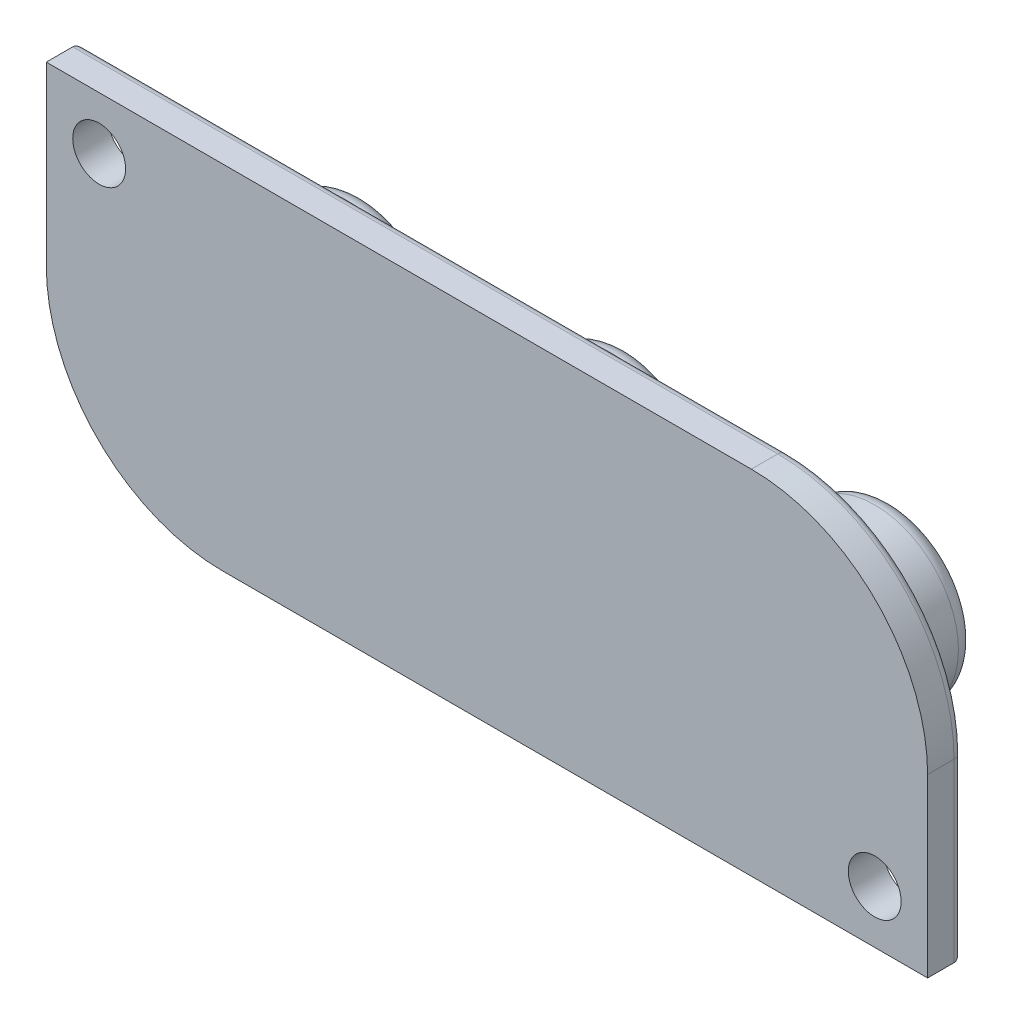
SolidWorks part; units mm, degrees
ref_plane "Alzado" through (0, 0, 0) normal (0, 0, 1) x (1, 0, 0)
ref_plane "Planta" through (0, 0, 0) normal (0, 1, 0) x (1, 0, 0)
ref_plane "Vista lateral" through (0, 0, 0) normal (1, 0, 0) x (0, 0, -1)
sketch "Croquis1" plane through (0, 0, 0) normal (0, 0, 1) x (1, 0, 0)
  line L4 (77.5, 27.5) -> (77.5, 24.2463) construction
  line L5 (52.5, 37.5) -> (102.5, 37.5)
  line L7 (52.5, 17.5) -> (102.5, 17.5)
  line L8 (102.5, 37.5) -> (102.5, 17.5)
  line L10 (52.5, 27.5) -> (102.5, 27.5) construction
  line L11 (52.5, 37.5) -> (52.5, 17.5)
  point P0 (92.5, 27.5)
  dimension "D1" = 20
  dimension "D2" = 50
extrude "Saliente-Extruir1" add sketch "Croquis1" along normal blind 2
sketch "Croquis2" plane through (0, 0, 0) normal (0, 0, -1) x (-1, 0, 0)
  line L0 (-92.5, 27.5) -> (-77.5, 27.5) construction
  circle A4 centre (-92.5, 27.5) radius 4.75
  circle A5 centre (-77.5, 27.5) radius 4.75
  circle A6 centre (-62.5, 27.5) radius 4.75
  dimension "D1" = 9.5
  dimension "D2" = 15
extrude "Saliente-Extruir2" add sketch "Croquis2" along normal blind 6
sketch "Croquis3" plane through (0, 0, 0) normal (0, 0, -1) x (-1, 0, 0)
  line L5 (-86.8264, 25) -> (-68.1736, 30) construction
  line L6 (-86.8264, 30) -> (-68.1736, 25) construction
  line L10 (-85.748, 30) -> (-87.7924, 30.8017) construction
  line L11 (-87.7924, 30.8017) -> (-86.8264, 30) construction
  line L12 (-86.8264, 30) -> (-86.6329, 30.8376) construction
  arc A0 (-87.3586, 30.0746) -> (-86.4645, 30.5224) centre (-86.9115, 30.2985) ccw
  arc A1 (-86.4645, 24.4776) -> (-87.3586, 24.9254) centre (-86.9115, 24.7015) ccw
  arc A2 (-82.6414, 24.9254) -> (-83.5355, 24.4776) centre (-83.0885, 24.7015) ccw
  arc A3 (-83.5355, 30.5224) -> (-82.6414, 30.0746) centre (-83.0885, 30.2985) ccw
  arc A4 (-67.6414, 24.9254) -> (-68.5355, 24.4776) centre (-68.0885, 24.7015) ccw
  arc A5 (-68.5355, 30.5224) -> (-67.6414, 30.0746) centre (-68.0885, 30.2985) ccw
  circle A14 centre (-62.5, 27.5) radius 5.75
  arc A15 (-67.6414, 24.9254) -> (-67.6414, 30.0746) centre (-62.5, 27.5) ccw
  circle A17 centre (-77.5, 27.5) radius 5.75
  arc A18 (-82.6414, 24.9254) -> (-82.6414, 30.0746) centre (-77.5, 27.5) ccw
  arc A19 (-86.4645, 30.5224) -> (-86.4645, 24.4776) centre (-92.5, 27.5) ccw
  circle A20 centre (-92.5, 27.5) radius 5.75
  arc A21 (-87.3586, 30.0746) -> (-87.3586, 24.9254) centre (-92.5, 27.5) ccw
  arc A22 (-83.5355, 24.4776) -> (-83.5355, 30.5224) centre (-77.5, 27.5) ccw
  arc A23 (-68.5355, 24.4776) -> (-68.5355, 30.5224) centre (-62.5, 27.5) ccw
  circle A24 centre (-62.5, 27.5) radius 5.75 construction
  circle A25 centre (-77.5, 27.5) radius 5.75 construction
  circle A26 centre (-62.5, 27.5) radius 6.75 construction
  circle A27 centre (-77.5, 27.5) radius 6.75 construction
  circle A28 centre (-92.5, 27.5) radius 6.75 construction
  circle A29 centre (-92.5, 27.5) radius 5.75 construction
  dimension "D5" = 5
  dimension "D1" = 1
  dimension "D2" = 1
  dimension "D3" = 1
  dimension "D4" = 1
extrude "Cortar-Extruir1" [suppressed] cut sketch "Croquis3" against normal up to surface (2 mm away)
fillet "Redondeo1" radius 10 2 edges at (52.5, 17.5, 1) (102.5, 37.5, 1)
sketch "Croquis6" [suppressed] plane through (0, 0, 2) normal (0, 0, 1) x (1, 0, 0)
  circle A0 centre (62.5, 27.5) radius 4.25
  circle A1 centre (77.5, 27.5) radius 4.25
  circle A2 centre (92.5, 27.5) radius 4.25
  arc A3 (67.6414, 30.0746) -> (67.6414, 24.9254) centre (62.5, 27.5) ccw construction
  dimension "D1" = 1.5
extrude "Cortar-Extruir3" [suppressed] cut sketch "Croquis6" against normal blind 7
sketch "Croquis9" [suppressed] plane through (0, 0, -5) normal (0, 0, 1) x (1, 0, 0)
  circle A0 centre (62.5, 27.5) radius 1.5
  circle A1 centre (77.5, 27.5) radius 1.5
  circle A2 centre (92.5, 27.5) radius 1.5
  dimension "D1" = 3
extrude "Saliente-Extruir3" [suppressed] add sketch "Croquis9" along normal blind 7
sketch "Croquis10" plane through (0, 0, 2) normal (0, 0, 1) x (1, 0, 0)
  line L8 (77.5, 27.5) -> (77.5, 42.4814) construction
  line L9 (77.5, 27.5) -> (69.2679, 27.5) construction
  line L10 (99.5, 20.5) -> (99.5, 17.5) construction
  line L11 (99.5, 20.5) -> (102.5, 20.5) construction
  line L12 (55.5, 34.5) -> (52.5, 34.5) construction
  line L13 (55.5, 34.5) -> (55.5, 37.5) construction
  circle A4 centre (99.5, 20.5) radius 1.5
  circle A5 centre (55.5, 34.5) radius 1.5
extrude "Cortar-Extruir5" cut sketch "Croquis10" against normal up to surface (2 mm away) up to face at (67.25, 27.5, 0)
sketch "Croquis11" [suppressed] plane through (0, 0, 0) normal (0, 0, -1) x (-1, 0, 0)
  line L0 (-83.5355, 24.4776) -> (-86.4645, 24.4776)
  line L1 (-68.5355, 30.5224) -> (-71.4645, 30.5224)
  line L2 (-83.5355, 30.5224) -> (-86.4645, 30.5224)
  line L3 (-68.5355, 24.4776) -> (-71.4645, 24.4776)
  arc A0 (-68.5355, 24.4776) -> (-68.5355, 30.5224) centre (-62.5, 27.5) ccw
  circle A1 centre (-62.5, 27.5) radius 5.75
  arc A2 (-83.5355, 24.4776) -> (-71.4645, 24.4776) centre (-77.5, 27.5) ccw
  circle A3 centre (-77.5, 27.5) radius 5.75
  arc A4 (-86.4645, 30.5224) -> (-86.4645, 24.4776) centre (-92.5, 27.5) ccw
  circle A5 centre (-92.5, 27.5) radius 6.2
  arc A6 (-71.4645, 30.5224) -> (-83.5355, 30.5224) centre (-77.5, 27.5) ccw
extrude "Cortar-Extruir6" [suppressed] cut sketch "Croquis11" against normal blind 1.2
chamfer "Chaflán1" [suppressed] distance 1 angle 45
sketch "Croquis12" plane through (0, 0, -6) normal (0, 0, -1) x (-1, 0, 0)
  text T0 "<r-45>A</r>" font "HelveticaNeue" height 5
  text T1 "<r-45>B</r>" font "HelveticaNeue" height 5
  text T2 "<r-45>C</r>" font "HelveticaNeue" height 5
extrude "Saliente-Extruir4" add sketch "Croquis12" along normal blind 0.5
fillet "Redondeo2" radius 2 3 edges at (97.25, 27.5, 0) (82.25, 27.5, 0) (67.25, 27.5, 0)
fillet "Redondeo3" radius 0.5 6 edges at (52.5, 32.5, 0) (55.4289, 20.4289, 0) (72.5, 37.5, 0) (99.5711, 34.5711, 0) (82.5, 17.5, 0) (102.5, 22.5, 0)
fillet "Redondeo4" radius 1 3 edges at (57.75, 27.5, -6) (72.75, 27.5, -6) (87.75, 27.5, -6)
